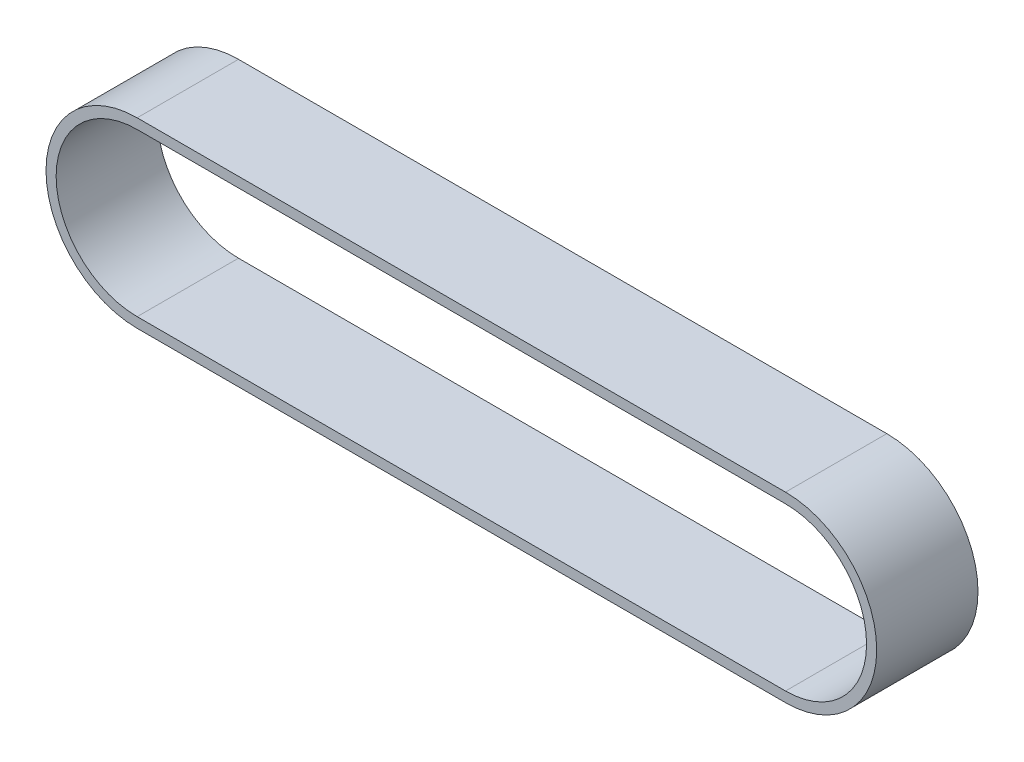
SolidWorks part; units mm, degrees
material "Rubber"
ref_plane "Front Plane" through (0, 0, 0) normal (0, 0, 1) x (1, 0, 0)
ref_plane "Top Plane" through (0, 0, 0) normal (0, 1, 0) x (1, 0, 0)
ref_plane "Right Plane" through (0, 0, 0) normal (1, 0, 0) x (0, 0, -1)
sketch "Sketch1" plane through (0, 0, 0) normal (0, 0, 1) x (1, 0, 0)
  line L0 (0, 40) -> (320, 40)
  line L1 (0, -40) -> (320, -40)
  line L2 (0, 45) -> (320, 45)
  line L3 (0, -45) -> (320, -45)
  arc A0 (0, 40) -> (0, -40) centre (0, 0) ccw
  arc A1 (320, -40) -> (320, 40) centre (320, 0) ccw
  arc A2 (320, -45) -> (320, 45) centre (320, 0) ccw
  arc A3 (0, 45) -> (0, -45) centre (0, 0) ccw
  dimension "D1" = 320
  dimension "D2" = 80
  dimension "D3" = 5
extrude "Boss-Extrude1" add sketch "Sketch1" along normal blind 50
